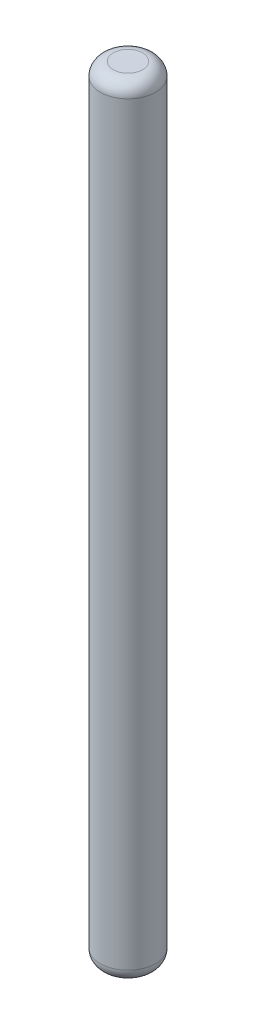
SolidWorks part; units mm, degrees
ref_plane "Front Plane" through (0, 0, 0) normal (0, 0, 1) x (1, 0, 0)
ref_plane "Top Plane" through (0, 0, 0) normal (0, 1, 0) x (1, 0, 0)
ref_plane "Right Plane" through (0, 0, 0) normal (1, 0, 0) x (0, 0, -1)
sketch "Sketch1" plane through (0, 0, 0) normal (0, 1, 0) x (1, 0, 0)
  circle A0 centre (0, 0) radius 2.125
  dimension "D1" = 4.25
extrude "Boss-Extrude1" add sketch "Sketch1" along normal blind 60
fillet "Fillet1" radius 1 2 edges at (0, 0, 2.125) (0, 60, 2.125)
